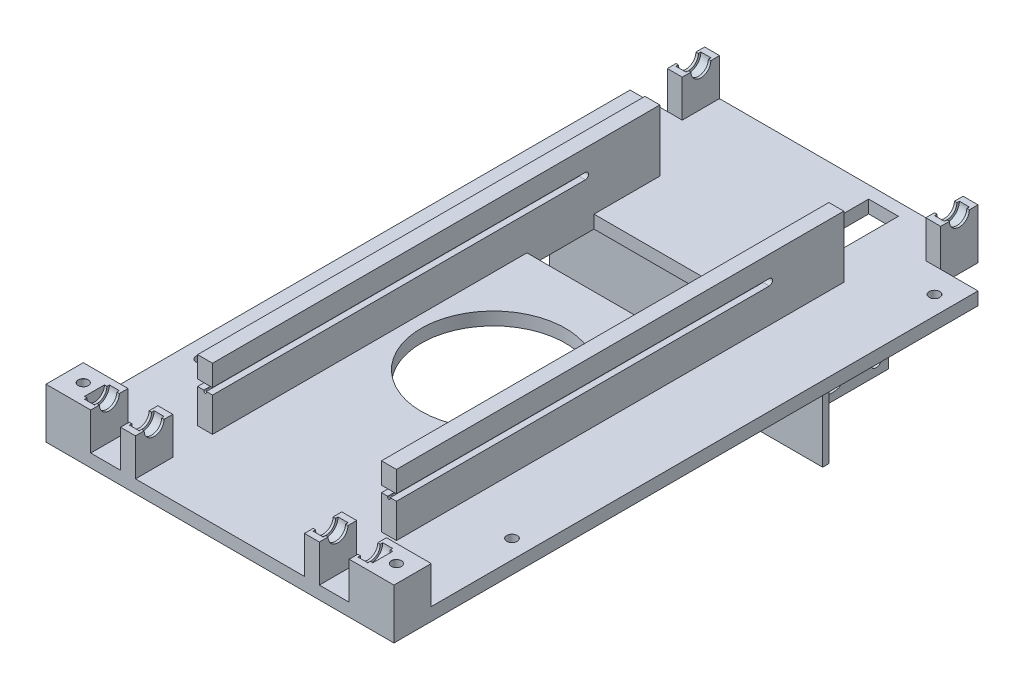
SolidWorks part; units mm, degrees
ref_plane "Front Plane" through (0, 0, 0) normal (0, 0, 1) x (1, 0, 0)
ref_plane "Top Plane" through (0, 0, 0) normal (0, 1, 0) x (1, 0, 0)
ref_plane "Right Plane" through (0, 0, 0) normal (1, 0, 0) x (0, 0, -1)
sketch "Sketch1" plane through (0, 0, 0) normal (0, 1, 0) x (1, 0, 0)
  line L1 (-70, -142.5) -> (70, -142.5)
  line L2 (-70, -127.5) -> (-70, 92.5)
  line L3 (-55, 107.5) -> (55, 107.5)
  line L4 (70, -117.5) -> (70, 92.5)
  line L5 (-60.2326, -127.5) -> (43.6981, 92.5) construction
  line L6 (-60.2326, 92.5) -> (83.0233, -127.5) construction
  line L9 (-70, 92.5) -> (-55, 92.5)
  line L10 (-55, 107.5) -> (-55, 92.5)
  line L13 (70, 92.5) -> (55, 92.5)
  line L14 (55, 107.5) -> (55, 92.5)
  line L18 (70, -142.5) -> (70, -117.5)
  line L22 (-70, -142.5) -> (-70, -127.5)
  point P0 (0, 0)
  dimension "D2" = 210
  dimension "D7" = 15
  dimension "D8" = 15
  dimension "D9" = 15
  dimension "D10" = 15
extrude "Boss-Extrude1" add sketch "Sketch1" along normal blind 5.2
sketch "Sketch2" plane through (0, 5.2, 0) normal (0, 1, 0) x (1, 0, 0)
  line L0 (55, 107.5) -> (-55, 107.5) construction
  circle A0 centre (0, -32.5) radius 29
  dimension "D1" = 58
  dimension "D2" = 140
extrude "Cut-Extrude1" cut sketch "Sketch2" against normal blind 5.2
sketch "Sketch5" plane through (0, 5.2, 0) normal (0, 1, 0) x (1, 0, 0)
  line L1 (55, 107.5) -> (49, 107.5)
  line L2 (55, 107.5) -> (55, 92.5)
  line L3 (55, 92.5) -> (49, 92.5)
  line L4 (49, 107.5) -> (49, 92.5)
  line L5 (-55, 107.5) -> (-49, 107.5)
  line L6 (-55, 107.5) -> (-55, 92.5)
  line L7 (-55, 92.5) -> (-49, 92.5)
  line L8 (-49, 107.5) -> (-49, 92.5)
  dimension "D1" = 15
  dimension "D2" = 6
  dimension "D3" = 6
  dimension "D4" = 15
extrude "Boss-Extrude3" add sketch "Sketch5" along normal blind 15
ref_plane "Plane1" through (0, 0, 0) normal (-1, 0, 0) x (0, 0, 1)
ref_plane "Plane2" through (-52, 0, 0) normal (-1, 0, 0) x (0, 0, 1)
sketch "Sketch8" plane through (-52, 0, 0) normal (-1, 0, 0) x (0, 0, 1)
  line L0 (-107.5, 20.2) -> (-92.5, 20.2) construction
  circle A0 centre (-100, 20.2) radius 5
  dimension "D1" = 10
extrude "Cut-Extrude3" cut sketch "Sketch8" against normal mid plane 4
mirror "Mirror1" about plane through (0, 0, 0) normal (-1, 0, 0) of "Cut-Extrude3"
sketch "Sketch9" plane through (-55, 0, 0) normal (-1, 0, 0) x (0, 0, 1)
  line L0 (-107.5, 20.2) -> (-92.5, 20.2) construction
  circle A0 centre (-100, 20.2) radius 4
  dimension "D1" = 8
extrude "Cut-Extrude4" cut sketch "Sketch9" against normal through all
sketch "Sketch3" plane through (0, 5.2, 0) normal (0, 1, 0) x (1, 0, 0)
  line L0 (-34, -32.5) -> (-34, -111.5)
  line L1 (-70, -142.5) -> (70, -142.5) construction
  line L2 (-34, -111.5) -> (-40, -111.5)
  line L3 (-40, -111.5) -> (-40, 68.5)
  line L4 (49, 107.5) -> (-49, 107.5) construction
  line L5 (-40, 68.5) -> (-34, 68.5)
  line L6 (-34, 68.5) -> (-34, -32.5)
  line L7 (0, -107.5) -> (0, 107.5) construction
  line L8 (40, 68.5) -> (34, 68.5)
  line L9 (34, 68.5) -> (34, -32.5)
  line L10 (34, -32.5) -> (34, -111.5)
  line L11 (34, -111.5) -> (40, -111.5)
  line L12 (40, -111.5) -> (40, 68.5)
  line L13 (-70, 92.5) -> (-70, -142.5) construction
  point P15 (0, 0)
  dimension "D1" = 6
  dimension "D2" = 34
  dimension "D3" = 180
  dimension "D4" = 30
  dimension "D5" = 31
extrude "Boss-Extrude2" add sketch "Sketch3" along normal blind 24.8
sketch "Sketch4" plane through (40, 0, 0) normal (1, 0, 0) x (0, 0, -1)
  line L0 (-111.5, 5.2) -> (68.5, 5.2) construction
  line L5 (-111.5, 20.2) -> (38.5, 20.2) construction
  line L6 (-111.5, 21.5) -> (38.5, 21.5)
  line L7 (-111.5, 18.9) -> (38.5, 18.9)
  line L8 (-111.5, 30) -> (-111.5, 5.2) construction
  arc A2 (-111.5, 21.5) -> (-111.5, 18.9) centre (-111.5, 20.2) ccw
  arc A3 (38.5, 18.9) -> (38.5, 21.5) centre (38.5, 20.2) ccw
  point P12 (-36.5, 20.2)
  dimension "D1" = 13.7
  dimension "D5" = 2.6
  dimension "D6" = 150
extrude "Cut-Extrude2" cut sketch "Sketch4" against normal through all
sketch "Sketch10" plane through (0, 0, 111.5) normal (0, 0, 1) x (1, 0, 0)
  line L2 (40, 18.9) -> (34, 18.9) construction
  line L3 (36.5, 18.5) -> (36.5, 18.9)
  line L4 (37.5, 18.5) -> (37.5, 18.9)
  line L5 (37.5, 18.9) -> (36.5, 18.9)
  arc A0 (36.5, 18.5) -> (37.5, 18.5) centre (37, 18.5) ccw
  dimension "D2" = 1
  dimension "D3" = 0.4
ref_plane "Plane3" through (37, 0, 0) normal (1, 0, 0) x (0, 0, -1)
sketch "Sketch11" plane through (37, 0, 0) normal (1, 0, 0) x (0, 0, -1)
  line L0 (-111.5, 18.5) -> (48.5038, 18.5)
  line L1 (38.5, 20.2) -> (-101.9032, 20.2) construction
  line L2 (-111.5, 21.9) -> (48.5038, 21.9)
  arc A0 (48.5038, 21.9) -> (48.5038, 18.5) centre (38.5, 20.2) cw
sweep "Cut-Sweep4" cut profiles "Sketch10" path edge at (40, 18.9, 36.5)
mirror "Mirror2" about plane through (0, 0, 0) normal (-1, 0, 0) of "Cut-Sweep4"
sketch "Sketch15" plane through (0, 5.2, 0) normal (0, 1, 0) x (1, 0, 0)
  line L0 (-34, -111.5) -> (-34, 68.5) construction
  line L1 (-34, 15) -> (34, 15)
  line L2 (-34, 15) -> (-34, 45)
  line L3 (-34, 45) -> (34, 45)
  line L4 (34, 15) -> (34, 45)
  line L5 (34, 68.5) -> (34, -111.5) construction
  dimension "D1" = 15
  dimension "D2" = 30
extrude "Cut-Extrude5" cut sketch "Sketch15" against normal blind 10
sketch "Sketch16" plane through (0, 0, 0) normal (0, -1, 0) x (1, 0, 0)
  line L1 (28, -47.5) -> (34, -47.5)
  line L2 (28, -47.5) -> (28, -92.5)
  line L3 (28, -92.5) -> (34, -92.5)
  line L4 (34, -47.5) -> (34, -92.5)
  line L5 (55, -107.5) -> (-55, -107.5) construction
  line L8 (70, 142.5) -> (70, -92.5) construction
  dimension "D1" = 45
  dimension "D2" = 15
  dimension "D3" = 6
  dimension "D4" = 36
extrude "Boss-Extrude4" add sketch "Sketch16" along normal blind 40
sketch "Sketch17" plane through (28, 0, 0) normal (-1, 0, 0) x (0, 0, 1)
  line L0 (-87.5, -5) -> (-87.5, -35) construction
  line L1 (-85.4, -5) -> (-85.4, -35)
  line L2 (-89.6, -5) -> (-89.6, -35)
  line L3 (-52.5, -5) -> (-52.5, -35) construction
  line L4 (-50.4, -5) -> (-50.4, -35)
  line L5 (-54.6, -5) -> (-54.6, -35)
  line L6 (-70, 0) -> (-70, -40) construction
  line L7 (-47.5, 0) -> (-92.5, 0) construction
  line L8 (-47.5, -40) -> (-92.5, -40) construction
  line L9 (-70, -10) -> (-70, -30) construction
  line L10 (-63, -10) -> (-63, -30)
  line L11 (-77, -10) -> (-77, -30)
  arc A0 (-85.4, -5) -> (-89.6, -5) centre (-87.5, -5) ccw
  arc A1 (-89.6, -35) -> (-85.4, -35) centre (-87.5, -35) ccw
  arc A2 (-50.4, -5) -> (-54.6, -5) centre (-52.5, -5) ccw
  arc A3 (-54.6, -35) -> (-50.4, -35) centre (-52.5, -35) ccw
  arc A4 (-63, -10) -> (-77, -10) centre (-70, -10) ccw
  arc A5 (-77, -30) -> (-63, -30) centre (-70, -30) ccw
  point P2 (-87.5, -20)
  point P9 (-52.5, -20)
  point P22 (-70, -20)
  dimension "D1" = 2.1
  dimension "D3" = 2.1
  dimension "D9" = 7
  dimension "D2" = 35
  dimension "D4" = 17.5
  dimension "D5" = 5
  dimension "D6" = 5
  dimension "D7" = 5
  dimension "D8" = 5
  dimension "D10" = 10
  dimension "D11" = 10
extrude "Cut-Extrude6" cut sketch "Sketch17" against normal blind 40
sketch "Sketch19" plane through (0, 0, 0) normal (0, -1, 0) x (1, 0, 0)
  line L1 (28, -62.5) -> (16, -62.5)
  line L2 (28, -62.5) -> (28, -102.5)
  line L3 (28, -102.5) -> (16, -102.5)
  line L4 (16, -62.5) -> (16, -102.5)
  line L5 (28, -47.5) -> (28, -92.5) construction
  line L6 (55, -107.5) -> (-55, -107.5) construction
  dimension "D1" = 12
  dimension "D2" = 40
  dimension "D3" = 5
extrude "Cut-Extrude7" cut sketch "Sketch19" against normal blind 40
sketch "Sketch20" plane through (0, 5.2, 0) normal (0, 1, 0) x (1, 0, 0)
sketch "Sketch22" plane through (0, 5.2, 0) normal (0, 1, 0) x (1, 0, 0)
  line L0 (-55, 92.5) -> (-70, 92.5) construction
  line L1 (-70, 92.5) -> (-70, -142.5) construction
  line L7 (70, -142.5) -> (70, 92.5) construction
  line L8 (70, 92.5) -> (55, 92.5) construction
  line L9 (-70, -142.5) -> (70, -142.5) construction
  point P0 (-62.5, 82.5)
  point P2 (62.5, 82.5)
  point P4 (62.5, -87.5)
  point P6 (-62.5, -87.5)
  dimension "D1" = 10
  dimension "D2" = 7.5
  dimension "D3" = 55
  dimension "D4" = 7.5
  dimension "D5" = 55
  dimension "D6" = 7.5
  dimension "D7" = 7.5
  dimension "D8" = 10
hole_wizard "Ø4.0mm Dowel Hole2" positions "Sketch22" profile "Sketch23" hole size "Ø4.0" standard "ANSI Metric" end condition through all
sketch "Sketch23" plane through (-62.5, 5.2, -82.5) normal (1, 0, 0) x (0, 0, 1)
  line L0 (0, 0) -> (0, 45.2)
  line L1 (0, 45.2) -> (2.1, 45.2)
  line L2 (2.1, 45.2) -> (2.1, 0)
  line L5 (2.1, 0) -> (0, 0)
  line L11 (0, -6.35) -> (0, 107.95) construction
  dimension "Thru Hole Dia." = 4.2
  dimension "Thru Hole Depth" = 45.2
sketch "Sketch24" plane through (0, 0, 0) normal (0, -1, 0) x (1, 0, 0)
  line L0 (34, -45) -> (-34, -45) construction
  line L1 (-55, -47.5) -> (55, -47.5)
  line L2 (-55, -47.5) -> (-55, -45)
  line L3 (-55, -45) -> (55, -45)
  line L4 (55, -47.5) -> (55, -45)
  line L5 (34, -47.5) -> (28, -47.5) construction
  line L6 (-55, -107.5) -> (-55, -92.5) construction
  line L7 (55, -92.5) -> (55, -107.5) construction
extrude "Boss-Extrude5" add sketch "Sketch24" along normal blind 40
sketch "Sketch25" plane through (0, 0, -45) normal (0, 0, 1) x (1, 0, 0)
  line L1 (-34, 5.2) -> (34, 5.2)
  line L2 (-34, 5.2) -> (-34, 0)
  line L3 (-34, 0) -> (34, 0)
  line L4 (34, 5.2) -> (34, 0)
extrude "Boss-Extrude6" add sketch "Sketch25" along normal blind 3
sketch "Sketch26" plane through (0, 5.2, 0) normal (0, 1, 0) x (1, 0, 0)
  line L0 (-70, -142.5) -> (70, -142.5) construction
  line L1 (-70, -142.5) -> (-52, -142.5)
  line L2 (-70, -142.5) -> (-70, -127.5)
  line L3 (-70, -127.5) -> (-52, -127.5)
  line L4 (-52, -142.5) -> (-52, -127.5)
  line L5 (70, -142.5) -> (52, -142.5)
  line L6 (70, -142.5) -> (70, -127.5)
  line L7 (70, -127.5) -> (52, -127.5)
  line L8 (52, -142.5) -> (52, -127.5)
  line L9 (-40, -142.5) -> (-34, -142.5)
  line L10 (-40, -142.5) -> (-40, -127.5)
  line L11 (-40, -127.5) -> (-34, -127.5)
  line L12 (-34, -142.5) -> (-34, -127.5)
  line L13 (-40, 68.5) -> (-40, -111.5) construction
  line L14 (34, -142.5) -> (40, -142.5)
  line L15 (34, -142.5) -> (34, -127.5)
  line L16 (34, -127.5) -> (40, -127.5)
  line L17 (40, -142.5) -> (40, -127.5)
  line L19 (40, -111.5) -> (40, 68.5) construction
  dimension "D1" = 6
  dimension "D2" = 15
  dimension "D3" = 15
  dimension "D5" = 6
  dimension "D6" = 15
  dimension "D7" = 15
  dimension "D8" = 12
  dimension "D9" = 12
extrude "Boss-Extrude7" add sketch "Sketch26" along normal blind 15
sketch "Sketch27" plane through (0, 0, 0) normal (-1, 0, 0) x (0, 0, 1)
  line L0 (127.5, 20.2) -> (142.5, 20.2) construction
  circle A0 centre (135, 20.2) radius 4
  dimension "D1" = 8
extrude "Cut-Extrude8" cut sketch "Sketch27" against normal mid plane 116
ref_plane "Plane4" through (-55, 0, 0) normal (1, 0, 0) x (0, 0, -1)
sketch "Sketch28" plane through (-55, 0, 0) normal (1, 0, 0) x (0, 0, -1)
  arc A0 (-139, 20.2) -> (-131, 20.2) centre (-135, 20.2) ccw construction
  arc A1 (-139, 20.2) -> (-131, 20.2) centre (-135, 20.2) ccw
  circle A2 centre (-135, 20.2) radius 5
  dimension "D1" = 10
extrude "Cut-Extrude9" cut sketch "Sketch28" against normal mid plane 4
pattern_linear "LPattern1" count 2 spacing 18 along (1, 0, 0) of "Cut-Extrude9"
pattern_linear "LPattern2" count 2 spacing 92 along (1, 0, 0) of "LPattern1", "Cut-Extrude9"
sketch "Sketch29" plane through (0, 20.2, 0) normal (0, 1, 0) x (1, 0, 0)
  line L0 (-70, -142.5) -> (-52, -142.5) construction
  line L1 (-70, -127.5) -> (-70, -142.5) construction
  line L2 (52, -142.5) -> (70, -142.5) construction
  line L3 (70, -142.5) -> (70, -127.5) construction
  point P0 (-63, -134.5)
  point P2 (63, -134.5)
  dimension "D1" = 8
  dimension "D2" = 7
  dimension "D3" = 8
  dimension "D4" = 7
hole_wizard "Ø4.0mm Dowel Hole1" positions "Sketch29" profile "Sketch30" hole size "Ø4.0" standard "ANSI Metric"
sketch "Sketch30" plane through (-63, 20.2, 134.5) normal (1, 0, 0) x (0, 0, 1)
  line L0 (0, 0) -> (0, 9.2017)
  line L1 (0, 9.2017) -> (2, 8)
  line L2 (2, 8) -> (2, 0.025)
  line L3 (2, 0.025) -> (2.025, 0)
  line L5 (2.025, 0) -> (0, 0)
  line L6 (-2, 0.025) -> (-2.025, 0) construction
  line L10 (0, 9.2017) -> (-2, 8) construction
  line L11 (0, -6.35) -> (0, 107.95) construction
  dimension "Hole Dia." = 4
  dimension "Hole Depth" = 8
  dimension "Near C'Sink Dia." = 4.05
  dimension "Near C'Sink Angle" = 90
  dimension "Drill Angle" = 118
